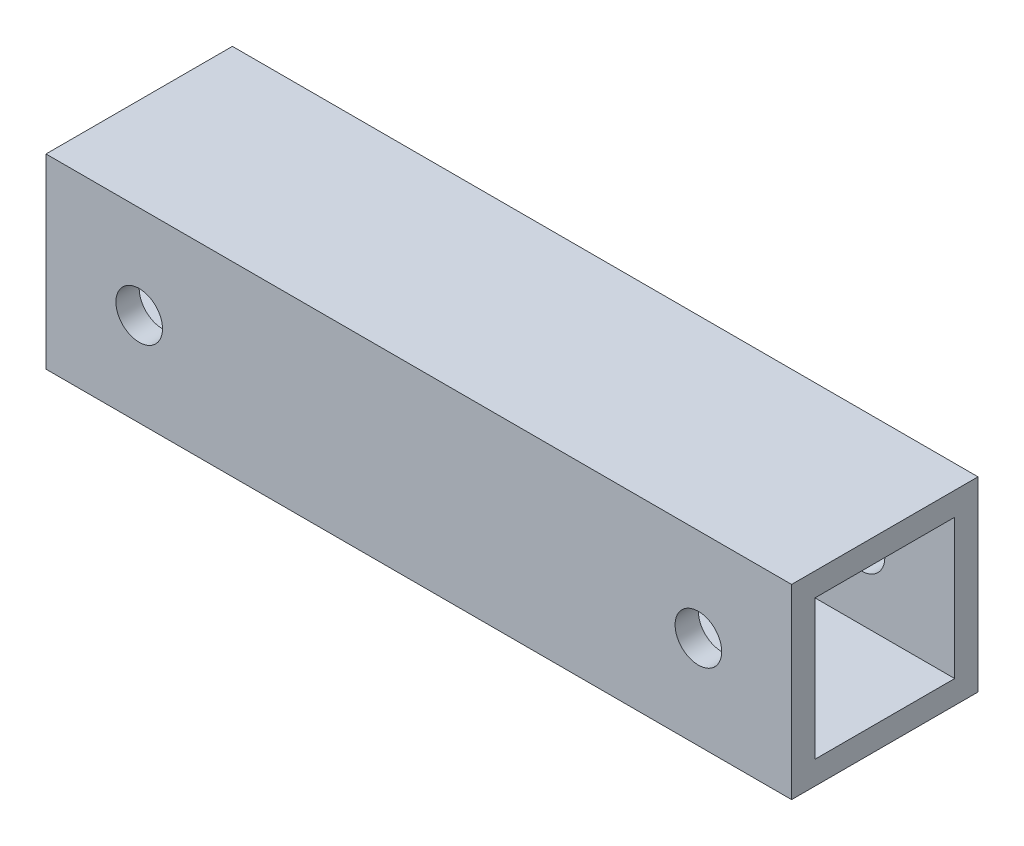
SolidWorks part; units mm, degrees
ref_plane "Front Plane" through (0, 0, 0) normal (0, 0, 1) x (1, 0, 0)
ref_plane "Top Plane" through (0, 0, 0) normal (0, 1, 0) x (1, 0, 0)
ref_plane "Right Plane" through (0, 0, 0) normal (1, 0, 0) x (0, 0, -1)
sketch "Sketch1" plane through (0, 0, 0) normal (0, 0, 1) x (1, 0, 0)
  line L1 (-50.8, -12.7) -> (50.8, -12.7)
  line L2 (-50.8, -12.7) -> (-50.8, 12.7)
  line L3 (-50.8, 12.7) -> (50.8, 12.7)
  line L4 (50.8, -12.7) -> (50.8, 12.7)
  line L5 (-50.8, -12.7) -> (50.8, 12.7) construction
  line L6 (-50.8, 12.7) -> (50.8, -12.7) construction
  point P0 (0, 0)
extrude "Boss-Extrude1" add sketch "Sketch1" along normal blind 25.4
sketch "Sketch2" plane through (50.8, 0, 0) normal (1, 0, 0) x (0, 0, -1)
  line L0 (-12.7, 12.7) -> (-12.7, -12.7)
  line L1 (-25.4, 12.7) -> (0, 12.7) construction
  line L2 (-25.4, -12.7) -> (0, -12.7) construction
  line L3 (-3.175, 9.5204) -> (-3.175, 12.7)
  line L4 (-22.225, -9.5204) -> (-3.175, -9.5204)
  line L5 (-22.225, -9.5204) -> (-22.225, 9.5204)
  line L6 (-22.225, 9.5204) -> (-3.175, 9.5204)
  line L7 (-3.175, -9.5204) -> (-3.175, 9.5204)
  line L8 (-22.225, -9.5204) -> (-3.175, 9.5204) construction
  line L9 (-22.225, 9.5204) -> (-3.175, -9.5204) construction
  line L10 (-3.175, 9.5204) -> (0, 9.5204)
  line L11 (0, -12.7) -> (0, 12.7) construction
  point P6 (-12.7, 0)
extrude "Cut-Extrude1" cut sketch "Sketch2" against normal blind 508 contours L6 L5 L4 L0 | L4 L7 L6 L0
sketch "Sketch4" plane through (0, 0, 25.4) normal (0, 0, 1) x (1, 0, 0)
  line L0 (-50.8, 0) -> (-38.1, 0)
  line L1 (-50.8, 12.7) -> (-50.8, -12.7) construction
  line L2 (50.8, 0) -> (38.1, 0)
  line L4 (50.8, -12.7) -> (50.8, 12.7) construction
  circle A0 centre (-38.1, 0) radius 3.175
  circle A1 centre (38.1, 0) radius 3.175
  point P11 (-38.2202, 0)
  point P12 (39.7696, 0)
extrude "Cut-Extrude3" cut sketch "Sketch4" against normal blind 508
